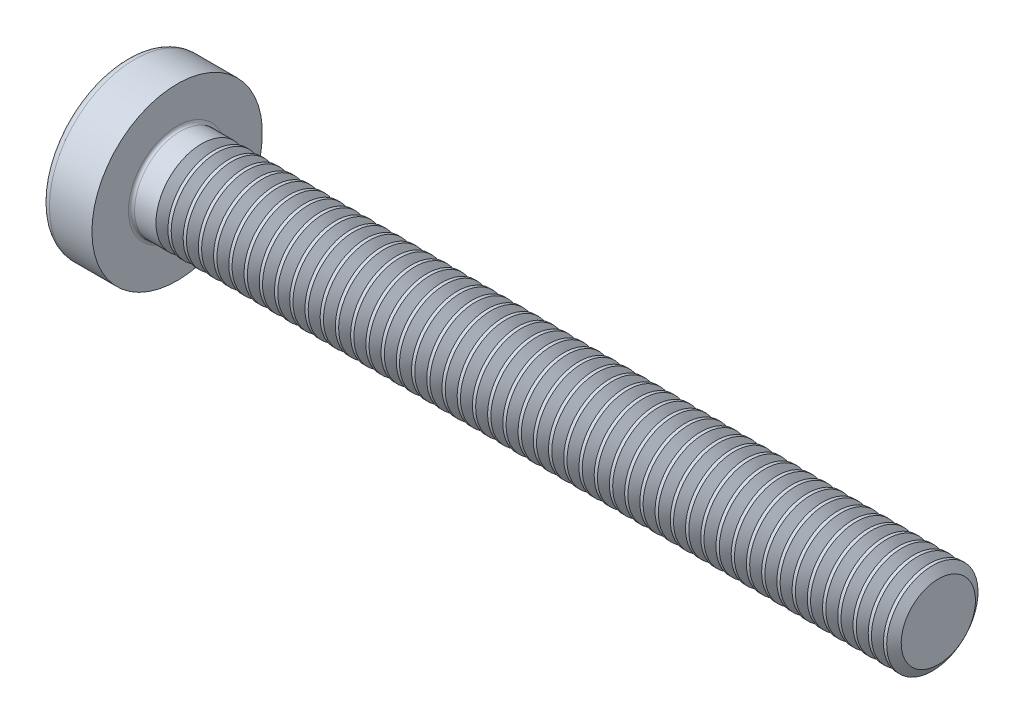
SolidWorks part; units mm, degrees
ref_plane "Plane1" through (0, 0, 0) normal (0, 0, 1) x (1, 0, 0)
ref_plane "Plane2" through (0, 0, 0) normal (0, 1, 0) x (1, 0, 0)
ref_plane "Plane3" through (0, 0, 0) normal (1, 0, 0) x (0, 0, -1)
sketch "BodySke" plane through (0, 0, 0) normal (0, 0, 1) x (1, 0, 0)
  line L0 (2.4, 1.5) -> (2.4, 2.8)
  line L1 (2.65, 6.35) -> (2.65, -3.175) construction
  line L2 (-25.4, 0) -> (127, 0) construction
  line L3 (27.4, 0) -> (0, 0)
  line L4 (2.4, 1.5) -> (27.4, 1.5)
  line L5 (27.4, 1.5) -> (27.4, 0)
  line L6 (1.0035, 2.8) -> (2.4, 2.8)
  line L8 (2.4, 6.35) -> (2.4, -3.175) construction
  arc A0 (0.7754, 2.6744) -> (0, 0) centre (5, 0) ccw
  arc A2 (0.7754, 2.6744) -> (1.0035, 2.8) centre (1.0035, 2.53) cw
  dimension "Head_crown_rad" = 5
  dimension "Head_fillet_rad" = 0.27
  dimension "Head_ht" = 2.4
  dimension "Head_dia" = 5.6
  dimension "Advance" = 0.5
  dimension "Diameter" = 3
revolve "Base-Revolve" add sketch "BodySke"
cosmetic thread "ThreadCosmetic" [suppressed]
fillet "Fillet1" radius 0.1 1 edges at (2.4, 0, 1.5)
sketch "Sketch3" plane through (0, 0, 0) normal (1, 0, 0) x (0, 0, -1)
  line L0 (0.37, -1.4) -> (-0.37, -1.4)
  line L1 (0.37, -1.4) -> (0.37, 1.4)
  line L2 (-0.37, 1.4) -> (0.37, 1.4)
  line L3 (-0.37, 1.4) -> (-0.37, -1.4)
  dimension "Cross_dia" = 2.8
  dimension "D1" = 1.4
  dimension "Cross_width" = 0.74
  dimension "D2" = 0.37
ref_plane "Plane4" through (1.75, 0, 0) normal (1, 0, 0) x (0, 0, -1)
sketch "Sketch4" plane through (1.75, 0, 0) normal (1, 0, 0) x (0, 0, -1)
  line L0 (0.37, -0.5275) -> (-0.37, -0.5275)
  line L1 (0.37, -0.5275) -> (0.37, 0.5275)
  line L2 (-0.37, 0.5275) -> (0.37, 0.5275)
  line L3 (-0.37, 0.5275) -> (-0.37, -0.5275)
  dimension "D1" = 0.74
  dimension "D2" = 1.055
  dimension "D3" = 0.37
  dimension "D4" = 0.5275
loft "Recess" cut profiles "Sketch3", "Sketch4"
pattern_circular "RecPat" count 2 every 90 about axis through (0, 0, 0) along (1, 0, 0) of "Recess"
sketch "RecCorSke" plane through (0, 0, 0) normal (0, 0, 1) x (1, 0, 0)
  line L0 (-3.175, 0) -> (15.875, 0) construction
  line L1 (-25.4, 0) -> (127, 0) construction
  line L2 (0, 0) -> (0, 0.6784)
  line L3 (0, 0.6784) -> (1.75, 0.556)
  line L4 (1.75, 0.556) -> (1.9307, 0)
  line L5 (1.9307, 0) -> (0, 0)
  dimension "Diameter" = 1.112
  dimension "Depth" = 1.75
  dimension "Draft_angle" = 4
  dimension "Bottom_angle" = 18
revolve "RecessCore" cut sketch "RecCorSke" angle 360 about L0
sketch "ThdSchSke" plane through (0, 0, 0) normal (0, 0, 1) x (1, 0, 0)
  line L0 (3.4, -1.2195) -> (3.2036, -1.5)
  line L1 (3.4, -1.2195) -> (3.5964, -1.5)
  line L2 (3.5964, -1.5) -> (3.5964, -1.875)
  line L3 (-3.175, 0) -> (5.1513, 0) construction
  line L5 (3.5964, -1.875) -> (3.2036, -1.875)
  line L6 (3.2036, -1.875) -> (3.2036, -1.5)
  dimension "Diameter" = 3
  dimension "SideAngle" = 55
  dimension "VeeAngle" = 70
  dimension "Thread_minor" = 2.439
  dimension "Overcut" = 3.75
  dimension "Start" = 3.4
revolve "ThreadSchematic" cut sketch "ThdSchSke" angle 360 about L3
pattern_linear "ThdSchPat" count 49 spacing 0.5 along (1, 0, 0) of "ThreadSchematic"
equation "\"D1@Sketch3\" = \"Cross_dia@Sketch3\" / 2"
equation "\"D2@Sketch3\" = \"Cross_width@Sketch3\" / 2"
equation "\"Depth@RecCorSke\" = \"Cross_depth@Plane4\""
equation "\"D1@Sketch4\" = \"Cross_width@Sketch3\""
equation "\"D2@Sketch4\" = \"Cross_dia@Sketch3\" - 2.0 * \"Cross_depth@Plane4\" * tan(26.5  * 0.017453292)"
equation "\"D3@Sketch4\" = \"D1@Sketch4\" / 2"
equation "\"D4@Sketch4\" = \"D2@Sketch4\" / 2"
equation "\"Thread_length@ThreadCosmetic\" = ((sgn( (\"Length@BodySke\" - \"Advance@BodySke\" * 2.0 ) - \"Thread_nom@BodySke\" )-1)*( (\"Length@BodySke\" - \"Advance@BodySke\" * 2.0 ) - \"Thread_nom@BodySke\" ))/-2+ \"Thread_nom@BodySke\""
equation "\"Thread_minor@ThdSchSke\" = \"Thread_minor@ThreadCosmetic\""
equation "\"Diameter@ThdSchSke\" = \"Diameter@BodySke\""
equation "\"Overcut@ThdSchSke\" = \"Diameter@BodySke\" * 1.25"
equation "\"Start@ThdSchSke\" = \"Head_ht@BodySke\" + \"Length@BodySke\" - \"Thread_length@ThreadCosmetic\"  '---Non-countersunk---"
equation "\"Num_threads@ThdSchPat\" = int( \"Thread_length@ThreadCosmetic\" / \"Advance@BodySke\" + 0.999 )  + 1"
equation "\"Advance@ThdSchPat\" = \"Thread_length@ThreadCosmetic\" /  (\"Num_threads@ThdSchPat\" - 1) 'relax it"
